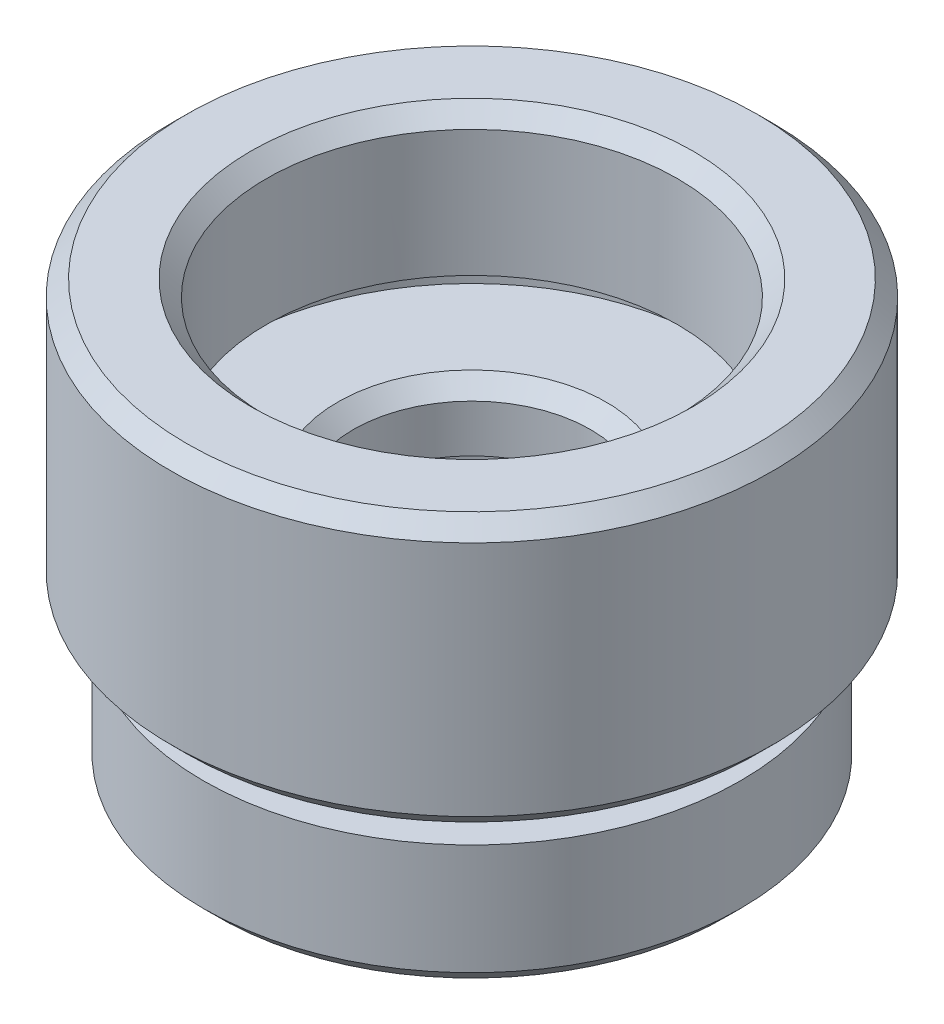
SolidWorks part; units mm, degrees
ref_plane "前视基准面" through (0, 0, 0) normal (0, 0, 1) x (1, 0, 0)
ref_plane "上视基准面" through (0, 0, 0) normal (0, 1, 0) x (1, 0, 0)
ref_plane "右视基准面" through (0, 0, 0) normal (1, 0, 0) x (0, 0, -1)
sketch "草图1" plane through (0, 0, 0) normal (0, 0, 1) x (1, 0, 0)
  line L0 (0, 0) -> (0, 51.3875) construction
  line L1 (2.75, 0) -> (2.75, 2)
  line L2 (2.75, 2) -> (3.15, 2)
  line L3 (3.15, 2) -> (3.15, 5)
  line L4 (3.15, 5) -> (4.85, 5)
  line L5 (4.85, 5) -> (4.85, 6)
  line L6 (4.85, 6) -> (3.75, 6)
  line L7 (3.75, 6) -> (3.75, 8)
  line L8 (3.75, 8) -> (7.6, 8)
  line L9 (2.75, 0) -> (8, 0)
  line L10 (7.6, 8) -> (7.6, 9)
  line L11 (7.6, 9) -> (6.5, 9)
  line L12 (6.5, 9) -> (6.5, 13.5)
  line L13 (6.5, 13.5) -> (9.025, 13.5)
  line L14 (0, 0) -> (5.8539, 0) construction
  line L15 (8.5, 0.5) -> (8.5, 4)
  line L16 (8.5, 4) -> (7, 4)
  line L17 (7, 4) -> (7, 5)
  line L18 (7, 5) -> (9.025, 5)
  line L19 (9.525, 5.5) -> (9.525, 13)
  line L20 (8, 0) -> (8.5, 0.5)
  line L21 (9.025, 5) -> (9.525, 5.5)
  line L22 (9.525, 13) -> (9.025, 13.5)
  point P13 (8.5, 0)
  point P22 (9.525, 5)
  point P24 (9.525, 13.5)
  dimension "D1" = 2.75
  dimension "D2" = 2
  dimension "D3" = 3.15
  dimension "D4" = 3
  dimension "D5" = 4.85
  dimension "D6" = 1
  dimension "D7" = 3.75
  dimension "D8" = 1
  dimension "D9" = 7.6
  dimension "D10" = 5.5
  dimension "D11" = 13.5
  dimension "D12" = 6.5
  dimension "D13" = 8.5
  dimension "D14" = 1
  dimension "D15" = 0.5
  dimension "D16" = 7
  dimension "D17" = 9.525
  dimension "D18" = 0.5
  dimension "D19" = 45
  dimension "D20" = 45
  dimension "D21" = 0.5
  dimension "D22" = 45
  dimension "D23" = 5
revolve "旋转1" add sketch "草图1" angle 360 about L0
cosmetic thread "装饰螺纹线1" parameters "D2"=15
cosmetic thread "装饰螺纹线2" parameters "D2"=15
cosmetic thread "装饰螺纹线3" parameters "D2"=9.5
chamfer "倒角1" distance 0.5 angle 45 2 edges at (0, 8, -3.75) (0, 13.5, -6.5)
